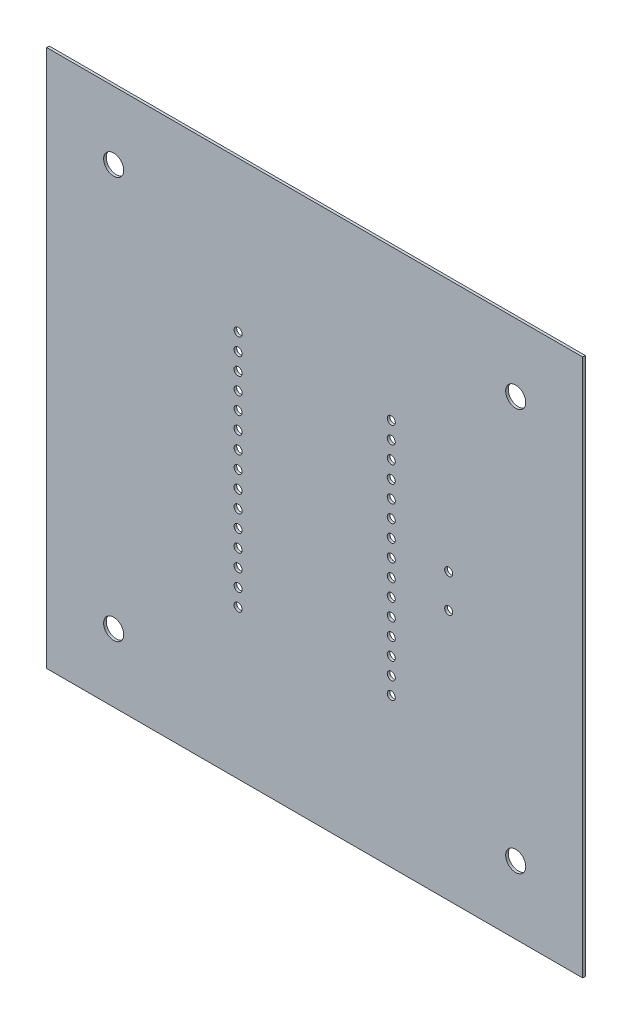
SolidWorks part; units mm, degrees
ref_plane "Plano frontal" through (0, 0, 0) normal (0, 0, 1) x (1, 0, 0)
ref_plane "Plano superior" through (0, 0, 0) normal (0, 1, 0) x (1, 0, 0)
ref_plane "Plano direito" through (0, 0, 0) normal (1, 0, 0) x (0, 0, -1)
sketch "Esboço1" plane through (0, 0, 0) normal (0, 0, 1) x (1, 0, 0)
  line L0 (0, 0) -> (80.005, 0)
  line L1 (80.005, 0) -> (80.005, 80.259)
  line L2 (80.005, 80.259) -> (0, 80.259)
  line L3 (0, 80.259) -> (0, 0)
extrude "Board" add sketch "Esboço1" along normal blind 0.3912
sketch "Esboço2" plane through (0, 0, 0.3912) normal (0, 0, 1) x (1, 0, 0)
  circle A0 centre (60, 37.5) radius 0.6
extrude "Hole - P1-1" cut sketch "Esboço2" against normal blind 0.3912
sketch "Esboço3" plane through (0, 0, 0.3912) normal (0, 0, 1) x (1, 0, 0)
  circle A0 centre (60, 42.5) radius 0.6
extrude "Hole - P1-2" cut sketch "Esboço3" against normal through all
sketch "Esboço4" plane through (0, 0, 0.3912) normal (0, 0, 1) x (1, 0, 0)
  circle A0 centre (51.43, 50.16) radius 0.6
extrude "Hole - P3-12" cut sketch "Esboço4" against normal through all
sketch "Esboço5" plane through (0, 0, 0.3912) normal (0, 0, 1) x (1, 0, 0)
  circle A0 centre (51.43, 52.7) radius 0.6
extrude "Hole - P3-13" cut sketch "Esboço5" against normal through all
sketch "Esboço6" plane through (0, 0, 0.3912) normal (0, 0, 1) x (1, 0, 0)
  circle A0 centre (51.43, 55.24) radius 0.6
extrude "Hole - P3-14" cut sketch "Esboço6" against normal through all
sketch "Esboço7" plane through (0, 0, 0.3912) normal (0, 0, 1) x (1, 0, 0)
  circle A0 centre (51.43, 57.78) radius 0.6
extrude "Hole - P3-15" cut sketch "Esboço7" against normal through all
sketch "Esboço8" plane through (0, 0, 0.3912) normal (0, 0, 1) x (1, 0, 0)
  circle A0 centre (51.43, 47.62) radius 0.6
extrude "Hole - P3-11" cut sketch "Esboço8" against normal through all
sketch "Esboço9" plane through (0, 0, 0.3912) normal (0, 0, 1) x (1, 0, 0)
  circle A0 centre (51.43, 45.08) radius 0.6
extrude "Hole - P3-10" cut sketch "Esboço9" against normal through all
sketch "Esboço10" plane through (0, 0, 0.3912) normal (0, 0, 1) x (1, 0, 0)
  circle A0 centre (51.43, 42.54) radius 0.6
extrude "Hole - P3-9" cut sketch "Esboço10" against normal through all
sketch "Esboço11" plane through (0, 0, 0.3912) normal (0, 0, 1) x (1, 0, 0)
  circle A0 centre (51.43, 40) radius 0.6
extrude "Hole - P3-8" cut sketch "Esboço11" against normal through all
sketch "Esboço12" plane through (0, 0, 0.3912) normal (0, 0, 1) x (1, 0, 0)
  circle A0 centre (51.43, 37.46) radius 0.6
extrude "Hole - P3-7" cut sketch "Esboço12" against normal through all
sketch "Esboço13" plane through (0, 0, 0.3912) normal (0, 0, 1) x (1, 0, 0)
  circle A0 centre (51.43, 34.92) radius 0.6
extrude "Hole - P3-6" cut sketch "Esboço13" against normal through all
sketch "Esboço14" plane through (0, 0, 0.3912) normal (0, 0, 1) x (1, 0, 0)
  circle A0 centre (51.43, 32.38) radius 0.6
extrude "Hole - P3-5" cut sketch "Esboço14" against normal through all
sketch "Esboço15" plane through (0, 0, 0.3912) normal (0, 0, 1) x (1, 0, 0)
  circle A0 centre (51.43, 22.22) radius 0.6
extrude "Hole - P3-1" cut sketch "Esboço15" against normal through all
sketch "Esboço16" plane through (0, 0, 0.3912) normal (0, 0, 1) x (1, 0, 0)
  circle A0 centre (51.43, 24.76) radius 0.6
extrude "Hole - P3-2" cut sketch "Esboço16" against normal through all
sketch "Esboço17" plane through (0, 0, 0.3912) normal (0, 0, 1) x (1, 0, 0)
  circle A0 centre (51.43, 27.3) radius 0.6
extrude "Hole - P3-3" cut sketch "Esboço17" against normal through all
sketch "Esboço18" plane through (0, 0, 0.3912) normal (0, 0, 1) x (1, 0, 0)
  circle A0 centre (51.43, 29.84) radius 0.6
extrude "Hole - P3-4" cut sketch "Esboço18" against normal through all
sketch "Esboço19" plane through (0, 0, 0.3912) normal (0, 0, 1) x (1, 0, 0)
  circle A0 centre (28.57, 50.16) radius 0.6
extrude "Hole - P2-12" cut sketch "Esboço19" against normal through all
sketch "Esboço20" plane through (0, 0, 0.3912) normal (0, 0, 1) x (1, 0, 0)
  circle A0 centre (28.57, 52.7) radius 0.6
extrude "Hole - P2-13" cut sketch "Esboço20" against normal through all
sketch "Esboço21" plane through (0, 0, 0.3912) normal (0, 0, 1) x (1, 0, 0)
  circle A0 centre (28.57, 55.24) radius 0.6
extrude "Hole - P2-14" cut sketch "Esboço21" against normal through all
sketch "Esboço22" plane through (0, 0, 0.3912) normal (0, 0, 1) x (1, 0, 0)
  circle A0 centre (28.57, 57.78) radius 0.6
extrude "Hole - P2-15" cut sketch "Esboço22" against normal through all
sketch "Esboço23" plane through (0, 0, 0.3912) normal (0, 0, 1) x (1, 0, 0)
  circle A0 centre (28.57, 47.62) radius 0.6
extrude "Hole - P2-11" cut sketch "Esboço23" against normal through all
sketch "Esboço24" plane through (0, 0, 0.3912) normal (0, 0, 1) x (1, 0, 0)
  circle A0 centre (28.57, 45.08) radius 0.6
extrude "Hole - P2-10" cut sketch "Esboço24" against normal through all
sketch "Esboço25" plane through (0, 0, 0.3912) normal (0, 0, 1) x (1, 0, 0)
  circle A0 centre (28.57, 42.54) radius 0.6
extrude "Hole - P2-9" cut sketch "Esboço25" against normal through all
sketch "Esboço26" plane through (0, 0, 0.3912) normal (0, 0, 1) x (1, 0, 0)
  circle A0 centre (28.57, 40) radius 0.6
extrude "Hole - P2-8" cut sketch "Esboço26" against normal through all
sketch "Esboço27" plane through (0, 0, 0.3912) normal (0, 0, 1) x (1, 0, 0)
  circle A0 centre (28.57, 37.46) radius 0.6
extrude "Hole - P2-7" cut sketch "Esboço27" against normal through all
sketch "Esboço28" plane through (0, 0, 0.3912) normal (0, 0, 1) x (1, 0, 0)
  circle A0 centre (28.57, 34.92) radius 0.6
extrude "Hole - P2-6" cut sketch "Esboço28" against normal through all
sketch "Esboço29" plane through (0, 0, 0.3912) normal (0, 0, 1) x (1, 0, 0)
  circle A0 centre (28.57, 32.38) radius 0.6
extrude "Hole - P2-5" cut sketch "Esboço29" against normal through all
sketch "Esboço30" plane through (0, 0, 0.3912) normal (0, 0, 1) x (1, 0, 0)
  circle A0 centre (28.57, 22.22) radius 0.6
extrude "Hole - P2-1" cut sketch "Esboço30" against normal through all
sketch "Esboço31" plane through (0, 0, 0.3912) normal (0, 0, 1) x (1, 0, 0)
  circle A0 centre (28.57, 24.76) radius 0.6
extrude "Hole - P2-2" cut sketch "Esboço31" against normal through all
sketch "Esboço32" plane through (0, 0, 0.3912) normal (0, 0, 1) x (1, 0, 0)
  circle A0 centre (28.57, 27.3) radius 0.6
extrude "Hole - P2-3" cut sketch "Esboço32" against normal through all
sketch "Esboço33" plane through (0, 0, 0.3912) normal (0, 0, 1) x (1, 0, 0)
  circle A0 centre (28.57, 29.84) radius 0.6
extrude "Hole - P2-4" cut sketch "Esboço33" against normal through all
sketch "Esboço34" plane through (0, 0, 0.3912) normal (0, 0, 1) x (1, 0, 0)
  line L0 (80.005, 0) -> (80.005, 80.259) construction
  line L1 (10.0025, 70.1295) -> (70.0025, 70.1295) construction
  line L2 (10.0025, 70.1295) -> (10.0025, 10.1295) construction
  line L3 (10.0025, 10.1295) -> (70.0025, 10.1295) construction
  line L4 (70.0025, 70.1295) -> (70.0025, 10.1295) construction
  line L5 (10.0025, 70.1295) -> (70.0025, 10.1295) construction
  line L6 (10.0025, 10.1295) -> (70.0025, 70.1295) construction
  line L7 (80.005, 80.259) -> (0, 80.259) construction
  circle A0 centre (10.0025, 70.1295) radius 1.5
  circle A1 centre (70.0025, 70.1295) radius 1.5
  circle A2 centre (70.0025, 10.1295) radius 1.5
  circle A3 centre (10.0025, 10.1295) radius 1.5
  point P0 (40.0025, 40.1295)
  point P8 (80.005, 40.1295)
  point P11 (40.0025, 80.259)
  dimension "D1" = 3
  dimension "D2" = 60
extrude "Free-Corte-extrusão33" cut sketch "Esboço34" against normal blind 10
